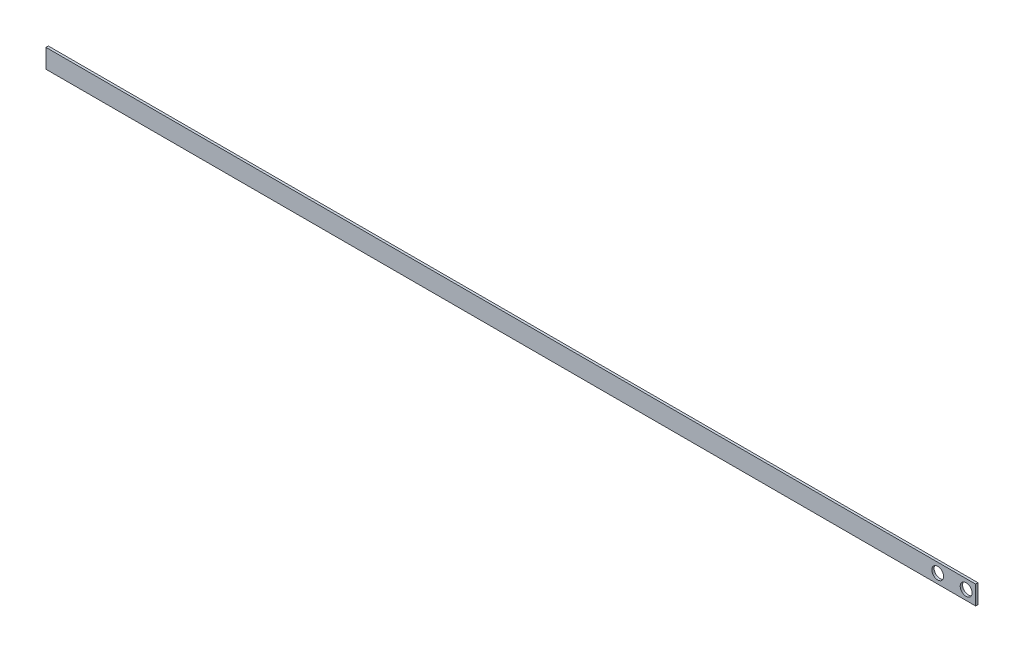
SolidWorks part; units mm, degrees
ref_plane "正面" through (0, 0, 0) normal (0, 0, 1) x (1, 0, 0)
ref_plane "平面" through (0, 0, 0) normal (0, 1, 0) x (1, 0, 0)
ref_plane "右側面" through (0, 0, 0) normal (1, 0, 0) x (0, 0, -1)
sketch "ｽｹｯﾁ1" plane through (0, 0, 0) normal (0, 0, 1) x (1, 0, 0)
  line L1 (0, 0) -> (196, 0)
  line L2 (0, 0) -> (0, -4)
  line L3 (0, -4) -> (196, -4)
  line L4 (196, 0) -> (196, -4)
  dimension "D1" = 196
  dimension "D2" = 4
extrude "ﾎﾞｽ - 押し出し1" add sketch "ｽｹｯﾁ1" along normal blind 0.5
sketch "ｽｹｯﾁ2" plane through (0, 0, 0.5) normal (0, 0, 1) x (1, 0, 0)
  line L0 (0, -2) -> (196, -2) construction
  line L1 (0, 0) -> (0, -4) construction
  line L2 (196, -4) -> (196, 0) construction
  circle A0 centre (188, -2) radius 1.25
  circle A1 centre (194, -2) radius 1.25
  dimension "D1" = 2.5
  dimension "D2" = 2.5
  dimension "D3" = 8
  dimension "D4" = 2
extrude "ｶｯﾄ - 押し出し1" cut sketch "ｽｹｯﾁ2" against normal blind 1
